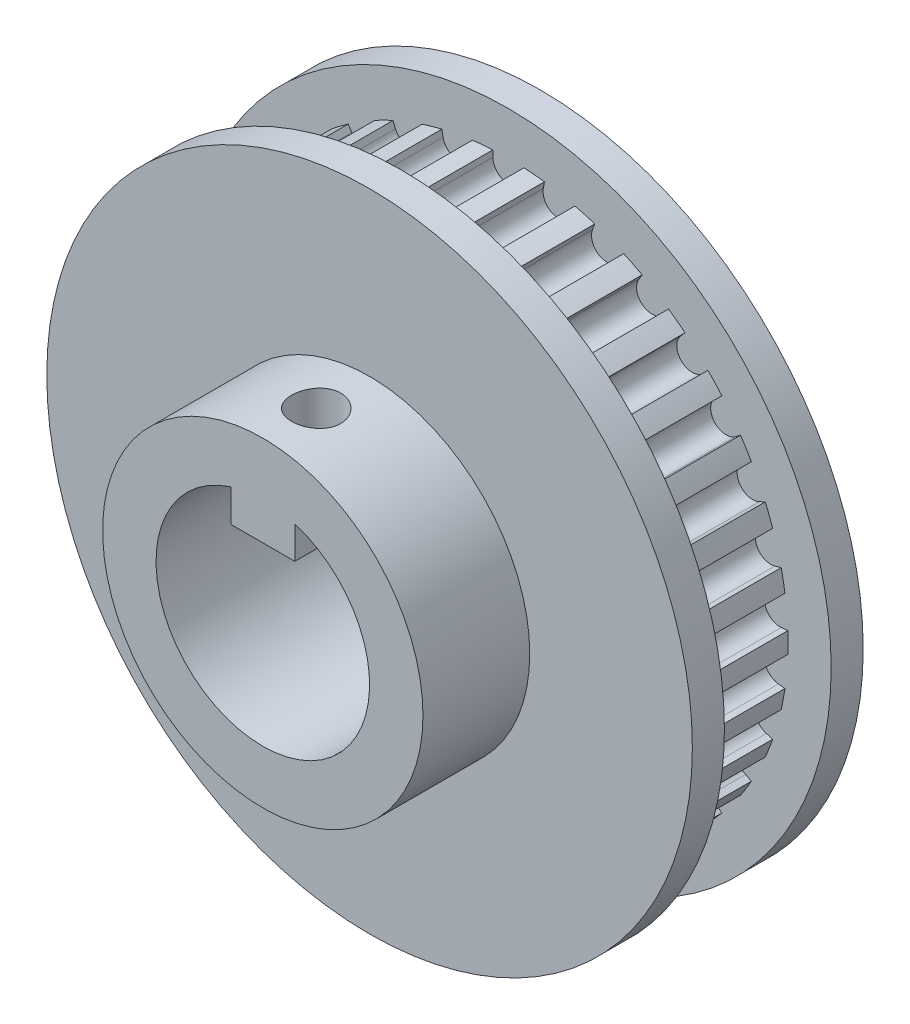
SolidWorks part; units mm, degrees
ref_plane "Front Plane" through (0, 0, 0) normal (0, 0, 1) x (1, 0, 0)
ref_plane "Top Plane" through (0, 0, 0) normal (0, 1, 0) x (1, 0, 0)
ref_plane "Right Plane" through (0, 0, 0) normal (1, 0, 0) x (0, 0, -1)
sketch "Sketch1" plane through (0, 0, 0) normal (0, 0, 1) x (1, 0, 0)
  line L3 (-1.4732, 27.9146) -> (1.4732, 27.9146) construction
  line L4 (0, 0) -> (0, 24.1046) construction
  line L5 (0, 24.1046) -> (0, 26.1874) construction
  line L6 (-1.4479, 25.5372) -> (-1.4732, 27.9146)
  line L7 (1.4479, 25.5372) -> (1.4732, 27.9146)
  line L8 (0, 26.1874) -> (0, 27.9146) construction
  circle A0 centre (0, 0) radius 27.051 construction
  circle A1 centre (0, 0) radius 30.23 construction
  arc A3 (-1.4479, 25.5372) -> (1.4479, 25.5372) centre (0, 25.5526) ccw
  point P11 (0, 27.051)
  point P13 (0, 30.23)
  dimension "D3" = 1.448
  dimension "D1" = 2.9464
  dimension "D2" = 3.81
sketch "Sketch2" plane through (0, 0, 0) normal (1, 0, 0) x (0, 0, -1)
  line L0 (-13, 10) -> (13, 10)
  line L1 (10, 26.1874) -> (10, 30.23)
  line L2 (-3, 15) -> (-13, 15)
  line L3 (13, 30.23) -> (10, 30.23)
  line L4 (-3, 30.23) -> (13, 30.23) construction
  line L5 (5, 30.23) -> (5, 26.1874) construction
  line L6 (0, 26.1874) -> (10, 26.1874)
  line L7 (0, 28.2087) -> (0, 30.23)
  line L8 (10, 28.2087) -> (10, 30.23) construction
  line L9 (13, 30.23) -> (13, 10)
  line L10 (-13, 0) -> (13, 0) construction
  line L11 (-13, 15) -> (-13, 10)
  line L12 (-3, 15) -> (-3, 30.23)
  line L13 (0, 30.23) -> (-1.5, 30.23)
  line L14 (17.1325, 30.23) -> (10, 30.23) construction
  line L15 (0, 26.1874) -> (0, 28.2087)
  line L16 (0, 28.2087) -> (0, 30.23) construction
  line L17 (0, 30.23) -> (-1.5, 30.23) construction
  line L18 (-1.5, 30.23) -> (-3, 30.23)
  point P25 (13, 0)
  point P26 (-3, 0)
  dimension "ID" = 20
  dimension "Hub Dia" = 30
  dimension "Outside Width" = 16
  dimension "Inside Width" = 10
  dimension "D2" = 60.46
revolve "Revolve1" add sketch "Sketch2" angle 360 mid plane about L10
sketch "Sketch3" plane through (0, 0, 0) normal (0, 0, 1) x (1, 0, 0)
  line L3 (-1.4479, 25.5372) -> (-1.4732, 27.9146) construction
  line L4 (1.4479, 25.5372) -> (1.4732, 27.9146) construction
  line L5 (-1.4479, 25.5372) -> (-1.4544, 26.147)
  line L6 (1.4479, 25.5372) -> (1.4544, 26.147)
  circle A0 centre (0, 0) radius 26.1874 construction
  arc A1 (1.4544, 26.147) -> (-1.4544, 26.147) centre (0, 0) ccw
  arc A3 (-1.4479, 25.5372) -> (1.4479, 25.5372) centre (0, 25.5526) ccw construction
  arc A4 (-1.4479, 25.5372) -> (1.4479, 25.5372) centre (0, 25.5526) ccw
extrude "Cut-Extrude1" cut sketch "Sketch3" against normal up to vertex (10 mm away) from vertex at 0 up to point (0, 26.1874, -10) starting at point (0, 26.1874, 0)
pattern_circular "CirPattern1" count 34 over 360 about axis through (0, 0, 0) along (0, 0, 1) of "Cut-Extrude1"
sketch "Sketch5" plane through (0, 0, 13) normal (0, 0, 1) x (1, 0, 0)
  line L0 (0, 0) -> (0, 8.25) construction
  line L1 (-3, 6.5) -> (3, 6.5)
  line L2 (-3, 6.5) -> (-3, 10)
  line L3 (-3, 10) -> (3, 10)
  line L4 (3, 6.5) -> (3, 10)
  line L5 (-3, 6.5) -> (3, 10) construction
  line L6 (-3, 10) -> (3, 6.5) construction
  circle A0 centre (0, 0) radius 10 construction
  point P0 (0, 8.25)
  dimension "D1" = 3.5
  dimension "D2" = 6
extrude "Boss-Extrude1" add sketch "Sketch5" against normal up to surface (26 mm away) up to face at (30.23, 0, -13)
ref_plane "Plane1" through (0, 15, 0) normal (0, 1, 0) x (1, 0, 0)
sketch "Sketch4" plane through (0, 15, 0) normal (0, 1, 0) x (1, 0, 0)
  line L0 (0, -3) -> (0, -13) construction
  line L1 (-15, -3) -> (15, -3) construction
  line L2 (-15, -13) -> (15, -13) construction
  circle A0 centre (0, -8) radius 2.3
  dimension "D1" = 4.6
extrude "Cut-Extrude2" cut sketch "Sketch4" against normal blind 10
equation "\"D2@Sketch2\" =  \"OD@Sketch1\""
